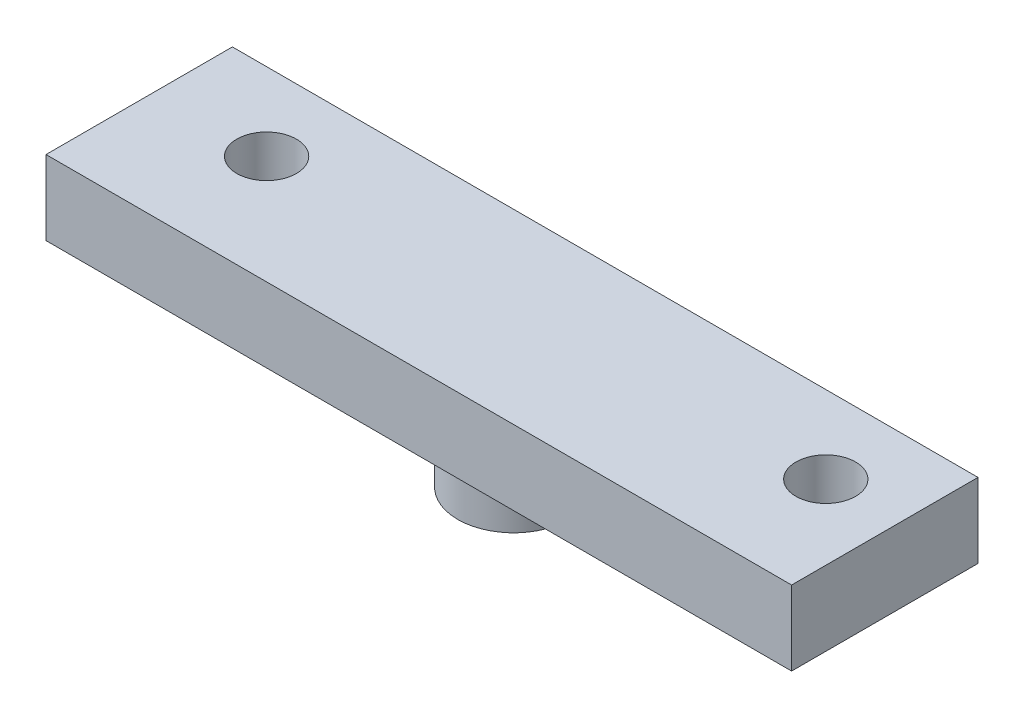
SolidWorks part; units mm, degrees
ref_plane "Front Plane" through (0, 0, 0) normal (0, 0, 1) x (1, 0, 0)
ref_plane "Top Plane" through (0, 0, 0) normal (0, 1, 0) x (1, 0, 0)
ref_plane "Right Plane" through (0, 0, 0) normal (1, 0, 0) x (0, 0, -1)
sketch "Sketch1" plane through (0, 0, 0) normal (0, 1, 0) x (1, 0, 0)
  line L1 (-0.3224, 3.46) -> (19.6776, 3.46)
  line L2 (-0.3224, 3.46) -> (-0.3224, -1.54)
  line L3 (-0.3224, -1.54) -> (19.6776, -1.54)
  line L4 (19.6776, 3.46) -> (19.6776, -1.54)
  circle A0 centre (17.6776, 1.3774) radius 0.8
  circle A1 centre (2.6776, 1.3774) radius 0.8
  dimension "D6" = 2
  dimension "D7" = 15
  dimension "D1" = 20
  dimension "D2" = 5
extrude "Boss-Extrude1" add sketch "Sketch1" along normal blind 2 contours A1 | A0 | L3 L4 L1 L2
sketch "Sketch2" plane through (0, 0, 0) normal (0, -1, 0) x (-1, 0, 0)
  line L0 (0.3224, 3.46) -> (0.3224, -1.54) construction
  circle A0 centre (-9.6776, 1.004) radius 1.5
  dimension "D1" = 10
extrude "Boss-Extrude2" add sketch "Sketch2" along normal blind 2
